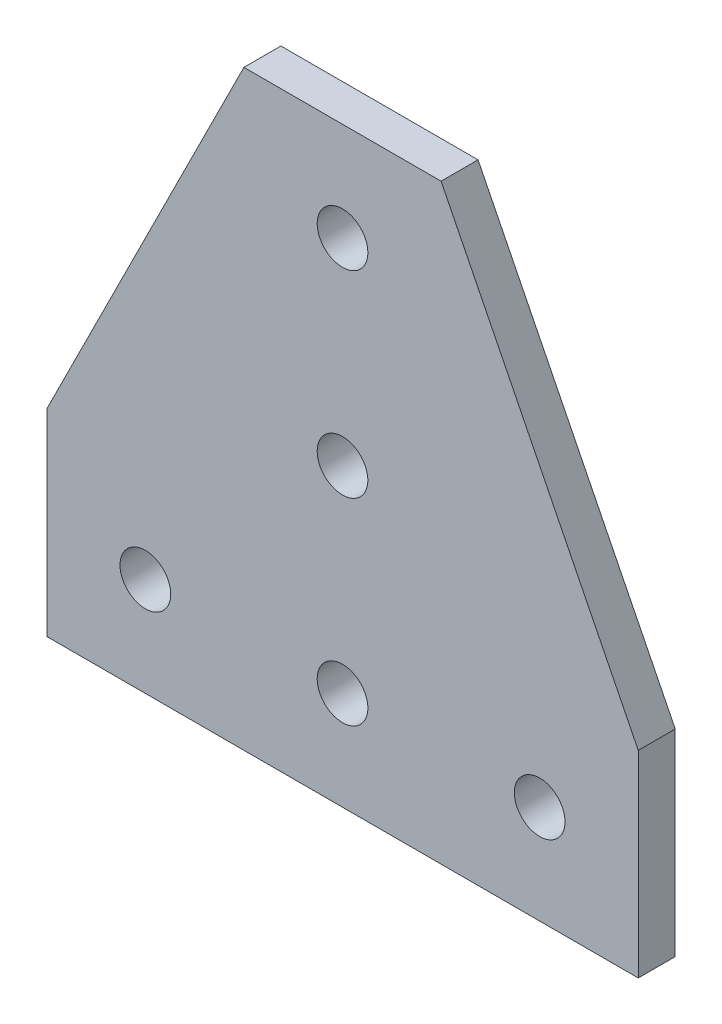
SolidWorks part; units mm, degrees
ref_plane "Front Plane" through (0, 0, 0) normal (0, 0, 1) x (1, 0, 0)
ref_plane "Top Plane" through (0, 0, 0) normal (0, 1, 0) x (1, 0, 0)
ref_plane "Right Plane" through (0, 0, 0) normal (1, 0, 0) x (0, 0, -1)
sketch "Sketch1" plane through (0, 0, 0) normal (0, 0, 1) x (1, 0, 0)
  line L0 (12.7, 25.4) -> (25.4, 25.4)
  line L1 (25.4, 25.4) -> (25.4, -50.8)
  line L2 (25.4, -50.8) -> (-12.7, -50.8)
  line L3 (-12.7, -50.8) -> (-12.7, -25.4)
  line L4 (-12.7, -25.4) -> (12.7, 25.4)
  dimension "D1" = 12.7
  dimension "height" = 76.2
  dimension "width" = 38.1
  dimension "flat" = 25.4
extrude "Extrude1" add sketch "Sketch1" against normal blind 4.7625
mirror "Mirror1" about plane through (25.4, 25.4, -4.7625) normal (1, 0, 0) of bodies 101
sketch "Sketch2" plane through (0, 0, -4.7625) normal (0, 0, -1) x (-1, 0, 0)
  line L0 (-25.4, 25.4) -> (-25.4, -38.1) construction
  line L1 (-38.1, 25.4) -> (-12.7, 25.4) construction
  line L2 (12.7, -38.1) -> (-25.4, -38.1) construction
  line L3 (12.7, -25.4) -> (12.7, -50.8) construction
  circle A0 centre (-25.4, -38.1) radius 3.2639
  circle A1 centre (0, -38.1) radius 3.2639
  circle A2 centre (25.4, -38.1) radius 3.2639
  circle A3 centre (-25.4, -12.7) radius 3.2639
  circle A4 centre (-25.4, 12.7) radius 3.2639
  dimension "hole" = 6.5278
  dimension "D2" = 25.4
  dimension "D3" = 25.4
  dimension "D4" = 25.4
  dimension "center to center" = 25.4
extrude "single 90" [suppressed] cut sketch "Sketch2" against normal through all
sketch "Sketch3" plane through (0, 0, -4.7625) normal (0, 0, -1) x (-1, 0, 0)
  line L0 (-63.5, -38.1) -> (12.7, -38.1) construction
  line L1 (-63.5, -25.4) -> (-63.5, -50.8) construction
  line L2 (12.7, -25.4) -> (12.7, -50.8) construction
  line L3 (-25.4, 25.4) -> (-25.4, -38.1) construction
  line L4 (-38.1, 25.4) -> (-12.7, 25.4) construction
  circle A0 centre (-25.4, -38.1) radius 3.2639
  circle A1 centre (-25.4, -12.7) radius 3.2639
  circle A2 centre (-25.4, 12.7) radius 3.2639
  circle A3 centre (-50.8, -38.1) radius 3.2639
  circle A4 centre (0, -38.1) radius 3.2639
  dimension "D1" = 6.5278
  dimension "D3" = 25.4
  dimension "D4" = 25.4
  dimension "D5" = 25.4
  dimension "center to center" = 25.4
extrude "single tee" cut sketch "Sketch3" against normal through all
sketch "Sketch4" [suppressed] plane through (0, 0, -6.35) normal (0, 0, -1) x (-1, 0, 0)
  line L0 (19.05, -76.2) -> (19.05, -57.15) construction
  line L1 (12.7, -25.4) -> (12.7, -50.8) construction
  line L2 (19.05, -57.15) -> (19.05, -38.1) construction
  line L3 (-114.3, 38.1) -> (-38.1, 38.1) construction
  line L4 (-38.1, 25.4) -> (-12.7, 25.4) construction
  line L5 (-38.1, 38.1) -> (-19.05, 38.1) construction
  line L6 (-76.2, 38.1) -> (-76.2, -66.675) construction
  line L7 (19.05, -66.675) -> (-76.2, -66.675) construction
  line L8 (19.05, -47.625) -> (-28.575, -47.625) construction
  line L9 (-28.575, 38.1) -> (-28.575, -47.625) construction
  circle A0 centre (-76.2, -66.675) radius 4.1656
  circle A1 centre (-28.575, -47.625) radius 4.1656
  circle A2 centre (-28.575, -66.675) radius 4.1656
  circle A3 centre (-76.2, -47.625) radius 4.1656
  circle A4 centre (-3.175, -47.625) radius 4.1656
  circle A5 centre (22.225, -47.625) radius 4.1656
  circle A6 centre (-3.175, -66.675) radius 4.1656
  circle A7 centre (22.225, -66.675) radius 4.1656
  circle A8 centre (-76.2, -22.225) radius 4.1656
  circle A9 centre (-76.2, 3.175) radius 4.1656
  circle A10 centre (-28.575, 3.175) radius 4.1656
  circle A11 centre (-28.575, -22.225) radius 4.1656
  dimension "D3" = 25.4
  dimension "D4" = 25.4
  dimension "D5" = 6.5278
  dimension "center to center" = 25.4
  dimension "D2" = 25.4
extrude "double 90" [suppressed] cut sketch "Sketch4" against normal through all
sketch "Sketch5" plane through (0, 0, -4.7625) normal (0, 0, -1) x (-1, 0, 0)
  line L0 (-25.4, 25.4) -> (-25.4, -50.8) construction
  line L1 (-38.1, 25.4) -> (-12.7, 25.4) construction
  line L2 (-25.4, 25.4) -> (-12.7, 25.4) construction
  line L3 (-19.05, 25.4) -> (-19.05, -44.45) construction
  line L4 (12.7, -50.8) -> (12.7, -38.1) construction
  line L5 (12.7, -25.4) -> (12.7, -50.8) construction
  line L6 (12.7, -38.1) -> (12.7, -25.4) construction
  line L7 (12.7, -31.75) -> (-19.05, -31.75) construction
  line L8 (12.7, -44.45) -> (-19.05, -44.45) construction
  line L9 (12.7, -50.8) -> (-63.5, -50.8) construction
  circle A0 centre (-19.05, -31.75) radius 3.2639
  circle A1 centre (-19.05, -44.45) radius 3.2639
  circle A2 centre (6.35, -44.45) radius 3.2639
  circle A3 centre (6.35, -31.75) radius 3.2639
  circle A4 centre (-19.05, -6.35) radius 3.2639
  circle A5 centre (-19.05, 19.05) radius 3.2639
  circle A6 centre (-31.75, -44.45) radius 3.2639
  circle A7 centre (-57.15, -44.45) radius 3.2639
  circle A8 centre (-57.15, -31.75) radius 3.2639
  circle A9 centre (-31.75, -31.75) radius 3.2639
  circle A10 centre (-31.75, -6.35) radius 3.2639
  circle A11 centre (-31.75, 19.05) radius 3.2639
  dimension "D2" = 25.4
  dimension "D3" = 25.4
  dimension "D1" = 6.5278
  dimension "center to center" = 25.4
extrude "double tee" [suppressed] cut sketch "Sketch5" against normal through all
ref_plane "Plane1" through (25.4, 9.4361, -4.7625) normal (-1, 0, 0) x (0, 0, 1)
equation "\"D2@Sketch2\" = \"center to center@Sketch2\""
equation "\"D3@Sketch2\" = \"center to center@Sketch2\""
equation "\"D4@Sketch2\" = \"center to center@Sketch2\""
equation "\"D1@Sketch3\" = \"hole@Sketch2\""
equation "\"D5@Sketch3\" = \"center to center@Sketch3\""
equation "\"D3@Sketch3\" = \"center to center@Sketch3\""
equation "\"D4@Sketch3\" = \"center to center@Sketch3\""
equation "\"D2@Sketch4\" = \"center to center@Sketch4\""
equation "\"D3@Sketch4\" = \"center to center@Sketch4\""
equation "\"D4@Sketch4\" = \"center to center@Sketch4\""
equation "\"D5@Sketch4\" = \"hole@Sketch2\""
equation "\"D1@Sketch5\" = \"hole@Sketch2\""
equation "\"D2@Sketch5\" = \"center to center@Sketch5\""
equation "\"D3@Sketch5\" = \"center to center@Sketch5\""
